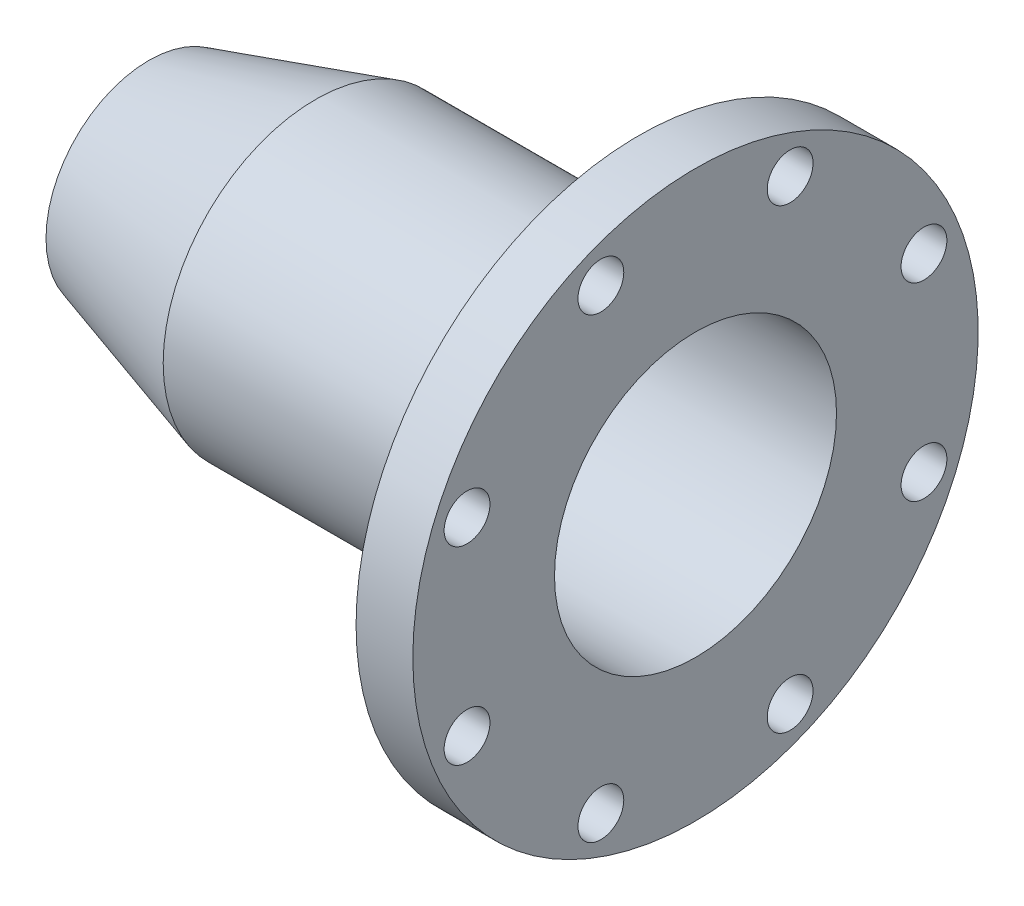
SolidWorks part; units mm, degrees
other "Camera1"
ref_plane "Front Plane" through (0, 0, 0) normal (0, 0, 1) x (1, 0, 0)
ref_plane "Top Plane" through (0, 0, 0) normal (0, 1, 0) x (1, 0, 0)
ref_plane "Right Plane" through (0, 0, 0) normal (1, 0, 0) x (0, 0, -1)
sketch "Sketch1" plane through (0, 0, 0) normal (0, 0, 1) x (1, 0, 0)
  line L0 (0, 0) -> (541.4119, 0) construction
  line L1 (266.7, 68.795) -> (266.7, 137.92)
  line L2 (266.7, 137.92) -> (239.01, 137.92)
  line L3 (239.01, 137.92) -> (239.01, 74.295)
  line L4 (239.01, 74.295) -> (81.28, 74.295)
  line L5 (239.01, 68.795) -> (82.0785, 68.795)
  line L6 (239.01, 68.795) -> (266.7, 68.795)
  line L7 (81.28, 74.295) -> (0, 50.1868)
  line L8 (82.0785, 68.795) -> (0, 44.45)
  line L9 (0, 50.1868) -> (0, 44.45)
  line L10 (239.01, 74.295) -> (266.7, 74.295)
  dimension "D2" = 27.69
  dimension "D3" = 74.295
  dimension "D4" = 185.42
  dimension "D5" = 266.7
  dimension "D6" = 5.5
  dimension "D7" = 5.5
  dimension "D1" = 44.45
revolve "Revolve1" add sketch "Sketch1" angle 360 about L0
sketch "Sketch3" plane through (266.7, 0, 0) normal (1, 0, 0) x (0, 0, -1)
  line L0 (0, 0) -> (0, 120.65) construction
  line L1 (0, 0) -> (-46.1708, 111.4661) construction
  circle A0 centre (0, 0) radius 120.65 construction
  dimension "D1" = 241.3
  dimension "D2" = 22.5
hole_wizard "1/16 (0.88) Diameter Hole1" positions "3DSketch2" profile "Sketch7" hole size "1/16" standard "ANSI Inch" end condition through all
sketch3d "3DSketch2"
  point P0 (266.7, 111.4661, 46.1708)
sketch "Sketch7" plane through (266.7, 111.4661, 46.1708) normal (0, 1, 0) x (0, 0, -1)
  line L0 (0, 0) -> (0, 266.7)
  line L1 (0, 266.7) -> (11.176, 266.7)
  line L2 (11.176, 266.7) -> (11.176, 0)
  line L5 (11.176, 0) -> (0, 0)
  line L11 (0, -6.35) -> (0, 107.95) construction
  dimension "Thru Hole Dia." = 22.352
  dimension "Thru Hole Depth" = 266.7
pattern_circular "CirPattern1" count 8 over 360 about axis through (0, 0, 0) along (1, 0, 0) of "1/16 (0.88) Diameter Hole1"
equation "\"Wall Thickness\"= 5.5"
equation "\"D6@Sketch1\"=\"Wall Thickness\""
equation "\"Nozzle diameter\"= 3.5 * 25.4"
equation "\"D7@Sketch1\"=\"Wall Thickness\""
equation "\"D1@Sketch1\"=\"Nozzle diameter\"/2"
